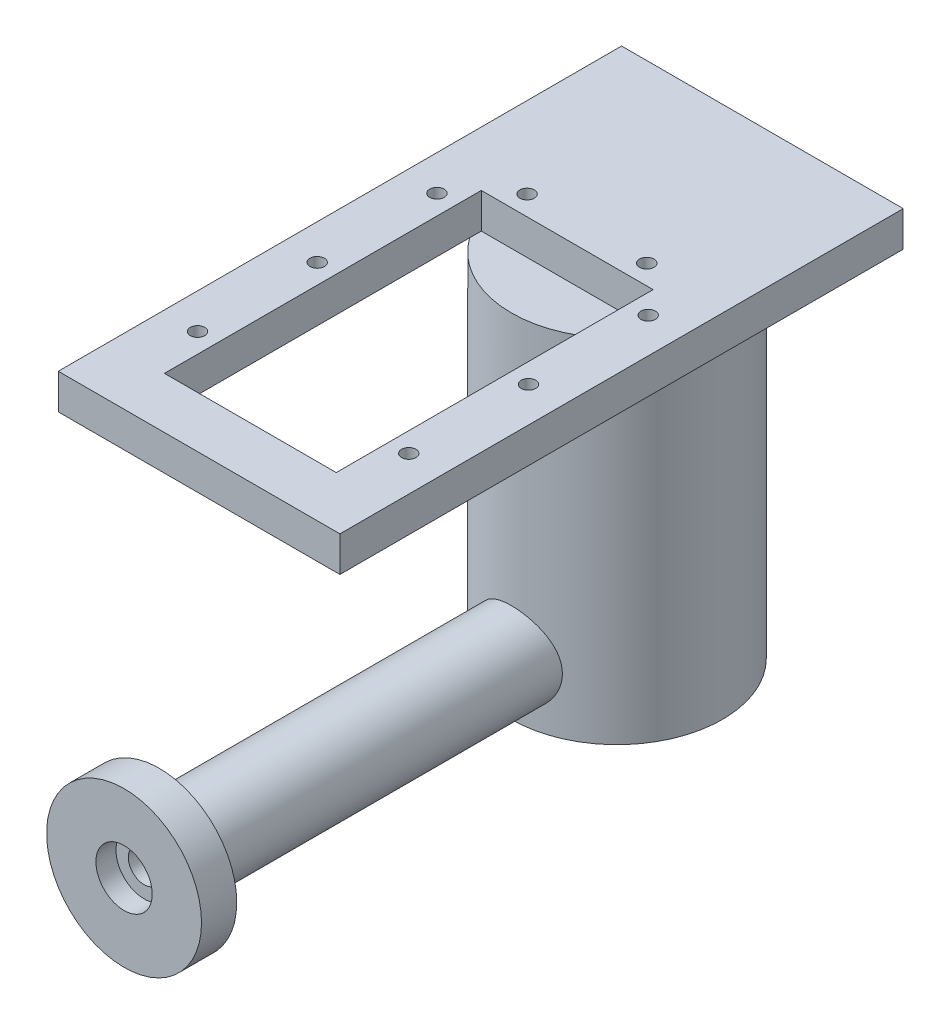
SolidWorks part; units mm, degrees
material "ABS"
ref_plane "Front Plane" through (0, 0, 0) normal (0, 0, 1) x (1, 0, 0)
ref_plane "Top Plane" through (0, 0, 0) normal (0, 1, 0) x (1, 0, 0)
ref_plane "Right Plane" through (0, 0, 0) normal (1, 0, 0) x (0, 0, -1)
sketch "Sketch1" plane through (0, 0, 0) normal (0, 1, 0) x (1, 0, 0)
  circle A0 centre (0, 0) radius 15
  dimension "D1" = 30
extrude "Boss-Extrude1" add sketch "Sketch1" along normal blind 50
ref_plane "Plane1" through (0, 0, 15) normal (0, 0, 1) x (1, 0, 0)
sketch "Sketch2" plane through (0, 0, 15) normal (0, 0, 1) x (1, 0, 0)
  circle A0 centre (0, 8) radius 6
  dimension "D1" = 12
  dimension "D2" = 8
extrude "Boss-Extrude2" add sketch "Sketch2" along normal blind 50 and the other way up to surface separate body other way up to face at (0, 50, 15)
sketch "Sketch6" plane through (0, 0, 65) normal (0, 0, 1) x (1, 0, 0)
  circle A0 centre (0, 8) radius 11
  dimension "D1" = 22
extrude "Boss-Extrude4" add sketch "Sketch6" along normal blind 5
sketch "Sketch7" plane through (0, 50, 0) normal (0, 1, 0) x (1, 0, 0)
  line L1 (-20, -59.3447) -> (20, -59.3447)
  line L2 (-20, -59.3447) -> (-20, 20.6553)
  line L3 (-20, 20.6553) -> (20, 20.6553)
  line L4 (20, -59.3447) -> (20, 20.6553)
  line L5 (-12.2, -52.068) -> (12.2, -52.068)
  line L6 (-12.2, -52.068) -> (-12.2, -7.068)
  line L7 (-12.2, -7.068) -> (12.2, -7.068)
  line L8 (12.2, -52.068) -> (12.2, -7.068)
  point P7 (0, -52.068)
  point P10 (0, -59.3447)
  dimension "D1" = 20
  dimension "D2" = 40
  dimension "D3" = 80
  dimension "D4" = 45
  dimension "D5" = 24.4
extrude "Boss-Extrude5" add sketch "Sketch7" along normal blind 5
sketch "Sketch8" plane through (0, 55, 0) normal (0, 1, 0) x (1, 0, 0)
  line L4 (-20, 20.6553) -> (-20, -59.3447)
  line L5 (-20, -59.3447) -> (20, -59.3447)
  line L6 (20, -59.3447) -> (20, 20.6553)
  line L7 (20, 20.6553) -> (-20, 20.6553)
  line L8 (-20, 20.6553) -> (-20, -59.3447)
  line L9 (-20, -59.3447) -> (20, -59.3447)
  line L10 (20, -59.3447) -> (20, 20.6553)
  line L11 (20, 20.6553) -> (-20, 20.6553)
  circle A0 centre (8.5, -4.268) radius 1.025
  circle A1 centre (15, -10.568) radius 1.025
  circle A2 centre (-8.5, -4.268) radius 1.025
  circle A3 centre (-15, -10.568) radius 1.025
  circle A4 centre (15, -27.568) radius 1.025
  circle A5 centre (15, -44.568) radius 1.025
  circle A6 centre (-15, -44.568) radius 1.025
  circle A7 centre (-15, -27.568) radius 1.025
  dimension "D1" = 0
extrude "Cut-Extrude3" cut sketch "Sketch8" against normal up to surface (5 mm away) contours A5 | A4 | A1 | A0 | A2 | A3 | A7 | A6 up to face at (0, 50, 19.3447)
sketch "Sketch9" plane through (0, 0, 70) normal (0, 0, 1) x (1, 0, 0)
  circle A0 centre (0, 8) radius 4
  circle A1 centre (0, 8) radius 11 construction
  dimension "D1" = 8
extrude "Cut-Extrude4" cut sketch "Sketch9" against normal blind 2.85
sketch "Sketch10" plane through (0, 0, 67.15) normal (0, 0, 1) x (1, 0, 0)
  circle A0 centre (0, 8) radius 2.25
  dimension "D1" = 4.5
extrude "Cut-Extrude5" cut sketch "Sketch10" against normal blind 2.5
